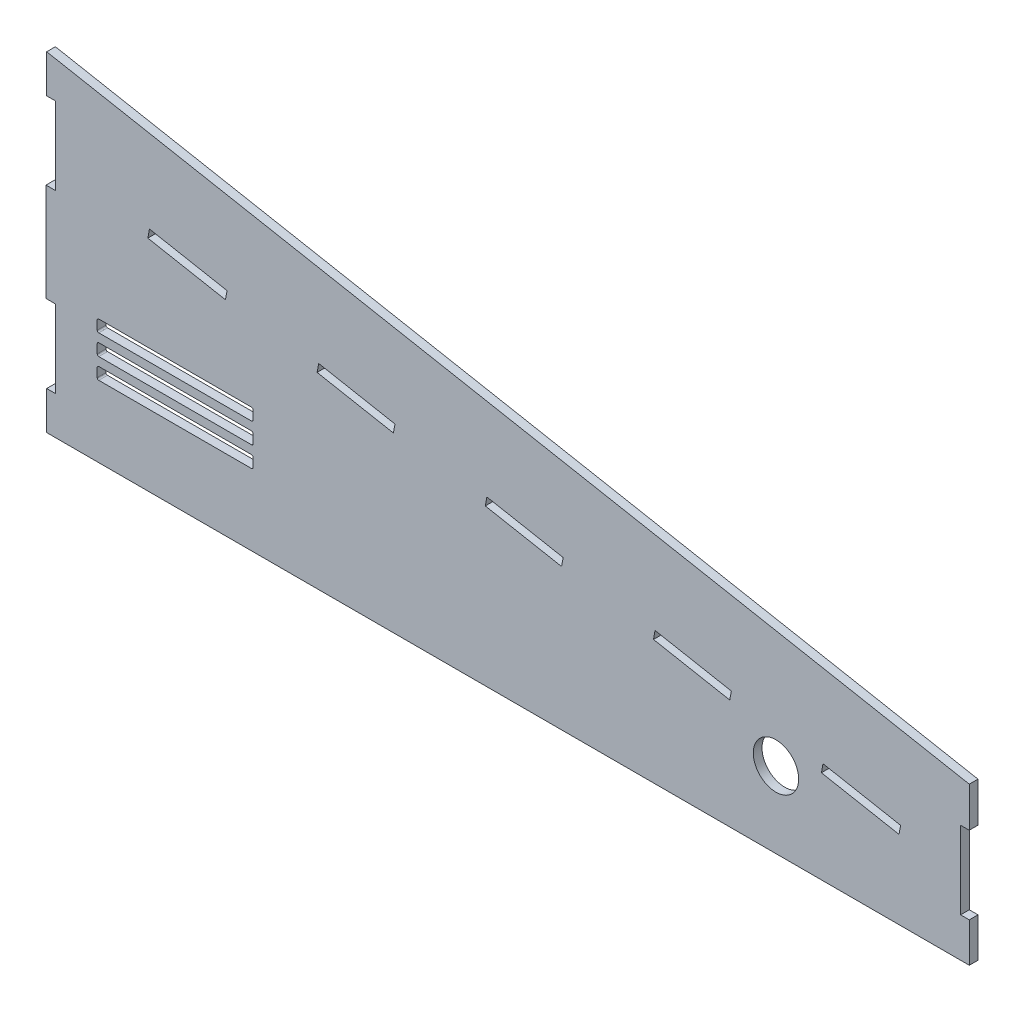
SolidWorks part; units mm, degrees
ref_plane "Front Plane" through (0, 0, 0) normal (0, 0, 1) x (1, 0, 0)
ref_plane "Top Plane" through (0, 0, 0) normal (0, 1, 0) x (1, 0, 0)
ref_plane "Right Plane" through (0, 0, 0) normal (1, 0, 0) x (0, 0, -1)
sketch "Sketch1" plane through (0, 0, 0) normal (0, 0, 1) x (1, 0, 0)
  line L5 (-159.8365, 166.0529) -> (-154.1365, 166.0529)
  line L6 (-159.8365, 0.1529) -> (-154.1365, 0.1529)
  line L9 (-154.1365, 0.1529) -> (-154.1365, 50.9529)
  line L10 (-159.8365, -24.8471) -> (-159.8365, 0.1529)
  line L11 (-154.1365, 50.9529) -> (-160.286, 50.9529)
  line L13 (-159.8365, 83.1029) -> (415.8968, 83.1029) construction
  line L14 (-154.1365, 115.2529) -> (-160.286, 115.2529)
  line L15 (-154.1365, 166.0529) -> (-154.1365, 115.2529)
  line L17 (-160.286, 115.2529) -> (-160.286, 50.9529)
  line L18 (-159.8365, 166.0529) -> (-159.8365, 191.0529)
  line L25 (144.9635, -24.8471) -> (144.9635, 133.9029) construction
  line L27 (-159.8365, 191.0529) -> (444.0635, 77.8217)
  line L29 (-159.8365, -24.8471) -> (444.0635, -24.8471)
  line L32 (444.0635, 51.6994) -> (444.0635, 77.8217)
  line L34 (444.0635, 51.6994) -> (438.3635, 51.6994)
  line L36 (438.3635, 51.6994) -> (438.3635, 0.8994)
  line L39 (444.0635, 0.8994) -> (438.3635, 0.8994)
  line L41 (444.0635, 0.8994) -> (444.0635, -24.8471)
  point P0 (0, 0)
  point P27 (438.3635, 26.2994)
  point P48 (144.9635, -18.7987)
  dimension "D2" = 25
  dimension "D3" = 5.7
  dimension "D4" = 5.7
  dimension "D5" = 215.9
  dimension "D6" = 107.95
  dimension "D7" = 50.8
extrude "Boss-Extrude1" add sketch "Sketch1" along normal blind 5.7
sketch "Sketch2" plane through (0, 0, 5.7) normal (0, 0, 1) x (1, 0, 0)
  line L0 (287.2612, 47.1294) -> (288.3117, 52.7318)
  line L1 (-154.1365, 166.0529) -> (-154.1365, 115.2529) construction
  line L3 (317.5237, 44.3547) -> (328.9237, 44.3547) construction
  line L4 (177.1791, 67.7705) -> (178.2296, 73.3729)
  line L6 (-92.5649, 124.199) -> (-41.7649, 114.6737)
  line L8 (144.7387, 76.7529) -> (-154.1365, 132.7939) construction
  line L9 (317.5237, 44.3547) -> (317.5237, 24.8466) construction
  line L12 (18.2176, 103.3761) -> (68.1475, 94.0139)
  line L14 (-24.7561, 42.1515) -> (-24.7561, 36.3014)
  line L15 (127.2493, 77.1326) -> (128.2997, 82.735)
  line L17 (153.2647, 78.0539) -> (152.7394, 75.2527) construction
  line L18 (348.3126, 41.5318) -> (347.2529, 35.8806)
  line L20 (-160.286, 115.2529) -> (-160.286, 50.9529) construction
  line L21 (238.3819, 62.0939) -> (237.3314, 56.4916)
  line L22 (288.3117, 52.7318) -> (238.3819, 62.0939)
  line L24 (347.2529, 35.8806) -> (398.0529, 26.3553)
  line L26 (399.1126, 32.0065) -> (348.3126, 41.5318)
  line L29 (287.2612, 47.1294) -> (237.3314, 56.4916)
  line L31 (17.1672, 97.7737) -> (67.097, 88.4116)
  line L32 (-93.6337, 118.499) -> (-42.8337, 108.9737)
  line L33 (398.0529, 26.3553) -> (399.1126, 32.0065)
  line L34 (128.2997, 82.735) -> (178.2296, 73.3729)
  line L35 (127.2493, 77.1326) -> (177.1791, 67.7705)
  line L36 (152.2142, 72.4516) -> (153.2647, 78.0539) construction
  line L37 (17.1672, 97.7737) -> (18.2176, 103.3761)
  line L38 (68.1475, 94.0139) -> (67.097, 88.4116)
  line L39 (-92.5649, 124.199) -> (-93.6337, 118.499)
  line L40 (-42.8337, 108.9737) -> (-41.7649, 114.6737)
  line L41 (-25.7561, 56.6041) -> (-125.7561, 56.6041)
  line L42 (-126.7561, 55.6041) -> (-126.7561, 49.7539)
  line L43 (-125.7561, 48.7539) -> (-25.7561, 48.7539)
  line L44 (-24.7561, 49.7539) -> (-24.7561, 55.6041)
  line L45 (-137.797, 45.9527) -> (-137.797, 48.7539) construction
  line L46 (-137.797, 45.9527) -> (-160.286, 45.9527) construction
  line L47 (-125.7561, 43.1515) -> (-25.7561, 43.1515)
  line L48 (-126.7561, 36.3014) -> (-126.7561, 42.1515)
  line L49 (-25.7561, 35.3014) -> (-125.7561, 35.3014)
  line L50 (-75.7561, 35.3014) -> (-75.7561, 32.5002) construction
  line L51 (-75.7561, 32.5002) -> (-160.286, 32.5002) construction
  line L52 (-25.7561, 29.699) -> (-125.7561, 29.699)
  line L53 (-126.7561, 28.699) -> (-126.7561, 22.8488)
  line L54 (-125.7561, 21.8488) -> (-25.7561, 21.8488)
  line L55 (-24.7561, 22.8488) -> (-24.7561, 28.699)
  circle A2 centre (317.5237, 24.8466) radius 14.85
  arc A3 (-25.7561, 56.6041) -> (-24.7561, 55.6041) centre (-25.7561, 55.6041) cw
  arc A4 (-25.7561, 48.7539) -> (-24.7561, 49.7539) centre (-25.7561, 49.7539) ccw
  arc A5 (-125.7561, 56.6041) -> (-126.7561, 55.6041) centre (-125.7561, 55.6041) ccw
  arc A6 (-126.7561, 49.7539) -> (-125.7561, 48.7539) centre (-125.7561, 49.7539) ccw
  arc A7 (-126.7561, 42.1515) -> (-125.7561, 43.1515) centre (-125.7561, 42.1515) cw
  arc A8 (-125.7561, 35.3014) -> (-126.7561, 36.3014) centre (-125.7561, 36.3014) cw
  arc A9 (-25.7561, 43.1515) -> (-24.7561, 42.1515) centre (-25.7561, 42.1515) cw
  arc A10 (-25.7561, 35.3014) -> (-24.7561, 36.3014) centre (-25.7561, 36.3014) ccw
  arc A11 (-25.7561, 29.699) -> (-24.7561, 28.699) centre (-25.7561, 28.699) cw
  arc A12 (-25.7561, 21.8488) -> (-24.7561, 22.8488) centre (-25.7561, 22.8488) ccw
  arc A13 (-125.7561, 29.699) -> (-126.7561, 28.699) centre (-125.7561, 28.699) ccw
  arc A14 (-126.7561, 22.8488) -> (-125.7561, 21.8488) centre (-125.7561, 22.8488) ccw
  point P39 (-24.7561, 56.6041)
  point P49 (-126.7561, 56.6041)
  point P65 (-126.7561, 35.3014)
  point P66 (-24.7561, 35.3014)
  point P82 (-24.7561, 29.699)
  point P83 (-126.7561, 29.699)
  dimension "D2" = 29.7
  dimension "D3" = 1
  dimension "D4" = 50.8
  dimension "D5" = 2.8012
  dimension "D6" = 2.8012
  dimension "D7" = 100
  dimension "D10" = 50.8
  dimension "D13" = 25.4
extrude "Cut-Extrude1" cut sketch "Sketch2" against normal through all
